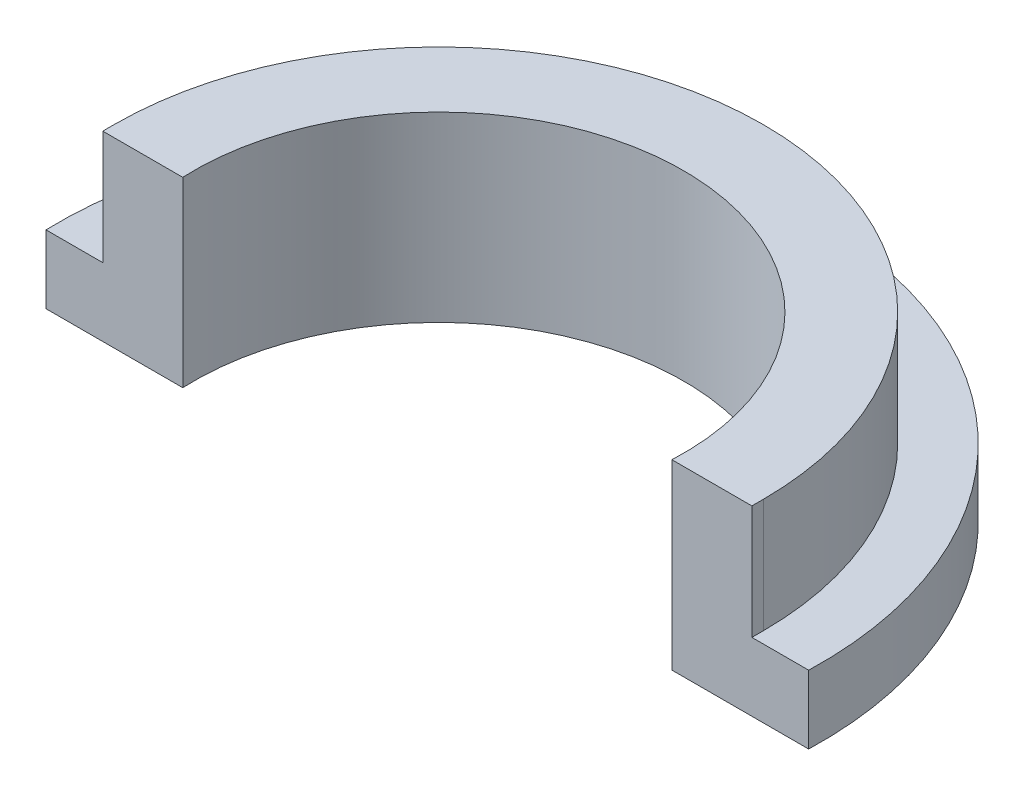
SolidWorks part; units mm, degrees
ref_plane "Front Plane" through (0, 0, 0) normal (0, 0, 1) x (1, 0, 0)
ref_plane "Top Plane" through (0, 0, 0) normal (0, 1, 0) x (1, 0, 0)
ref_plane "Right Plane" through (0, 0, 0) normal (1, 0, 0) x (0, 0, -1)
sketch "Sketch1" plane through (0, 0, 0) normal (0, 1, 0) x (1, 0, 0)
  line L0 (-13, 0) -> (-9, 0)
  line L1 (9, 0) -> (13, 0)
  circle A0 centre (0, 0) radius 12.43 construction
  circle A1 centre (0, 0) radius 9.43 construction
  circle A2 centre (0, 0) radius 13 construction
  circle A3 centre (0, 0) radius 9 construction
  arc A4 (9, 0) -> (-9, 0) centre (0, 0) ccw
  arc A5 (13, 0) -> (-13, 0) centre (0, 0) ccw
  dimension "D1" = 18.86
  dimension "D2" = 24.86
  dimension "D3" = 26
  dimension "D4" = 18
sketch "Sketch4" plane through (0, 0, 0) normal (0, 1, 0) x (1, 0, 0)
  line L0 (9, 0) -> (13, 0) construction
  line L1 (-13, 0) -> (-9, 0) construction
  line L2 (9, 0) -> (13, 0)
  line L3 (-13, 0) -> (-9, 0)
  line L4 (-13.394, -0.4) -> (-8.5907, -0.4)
  line L5 (8.5907, -0.4) -> (13.394, -0.4)
  arc A0 (13, 0) -> (-13, 0) centre (0, 0) ccw construction
  arc A1 (9, 0) -> (-9, 0) centre (0, 0) ccw construction
  arc A2 (13, 0) -> (-13, 0) centre (0, 0) ccw
  arc A3 (9, 0) -> (-9, 0) centre (0, 0) ccw
  arc A4 (8.5907, -0.4) -> (-8.5907, -0.4) centre (0, 0) ccw
  arc A5 (13.394, -0.4) -> (-13.394, -0.4) centre (0, 0) ccw
  dimension "D1" = 0.4
extrude "Boss-Extrude2" add sketch "Sketch4" along normal blind 2
sketch "Sketch5" plane through (0, 2, 0) normal (0, 1, 0) x (1, 0, 0)
  line L0 (-11.4, 0) -> (-11.4, -0.4)
  line L1 (-13.394, -0.4) -> (-8.5907, -0.4) construction
  line L2 (-11.4, -0.4) -> (-8.5907, -0.4)
  line L3 (-11, 0) -> (-9, 0)
  line L4 (8.5907, -0.4) -> (11.4, -0.4)
  line L5 (8.5907, -0.4) -> (13.394, -0.4) construction
  line L6 (11.4, -0.4) -> (11.4, 0)
  line L7 (9, 0) -> (11, 0)
  arc A0 (8.5907, -0.4) -> (-8.5907, -0.4) centre (0, 0) ccw construction
  arc A1 (9, 0) -> (-9, 0) centre (0, 0) ccw construction
  arc A2 (8.5907, -0.4) -> (-8.5907, -0.4) centre (0, 0) ccw
  arc A3 (9, 0) -> (-9, 0) centre (0, 0) ccw
  arc A4 (11.4, 0) -> (-11.4, 0) centre (0, 0) ccw
  arc A5 (11, 0) -> (-11, 0) centre (0, 0) ccw
  dimension "D1" = 2
  dimension "D2" = 0.4
extrude "Boss-Extrude3" add sketch "Sketch5" along normal blind 4
sketch "Sketch6" plane through (0, 2, 0) normal (0, 1, 0) x (1, 0, 0)
  line L0 (-13.394, -0.4) -> (-11.4, -0.4)
  line L1 (-11.4, -0.4) -> (-11.4, 0)
  line L2 (13.394, -0.4) -> (11.4, -0.4)
  line L3 (11.4, -0.4) -> (11.4, 0)
  arc A0 (11.4, 0) -> (-11.4, 0) centre (0, 0) ccw construction
  arc A1 (13.394, -0.4) -> (-13.394, -0.4) centre (0, 0) ccw construction
  arc A2 (11.4, 0) -> (-11.4, 0) centre (0, 0) ccw
  arc A3 (13.394, -0.4) -> (-13.394, -0.4) centre (0, 0) ccw
extrude "Boss-Extrude4" add sketch "Sketch6" along normal blind 0.4
sketch "Sketch8" plane through (0, 6, 0) normal (0, 1, 0) x (1, 0, 0)
  line L0 (11.4, 0) -> (11.4, -0.4) construction
  line L1 (8.5907, -0.4) -> (11.4, -0.4) construction
  line L2 (-11.4, -0.4) -> (-8.5907, -0.4) construction
  line L3 (-11.4, -0.4) -> (-11.4, 0) construction
  line L4 (11.4, 0) -> (11.4, -0.4)
  line L5 (8.5907, -0.4) -> (11.4, -0.4)
  line L6 (-11.4, -0.4) -> (-8.5907, -0.4)
  line L7 (-11.4, -0.4) -> (-11.4, 0)
  arc A0 (8.5907, -0.4) -> (-8.5907, -0.4) centre (0, 0) ccw construction
  arc A1 (11.4, 0) -> (-11.4, 0) centre (0, 0) ccw construction
  arc A2 (8.5907, -0.4) -> (-8.5907, -0.4) centre (0, 0) ccw
  arc A3 (11.4, 0) -> (-11.4, 0) centre (0, 0) ccw
extrude "Boss-Extrude6" add sketch "Sketch8" along normal blind 0.4
